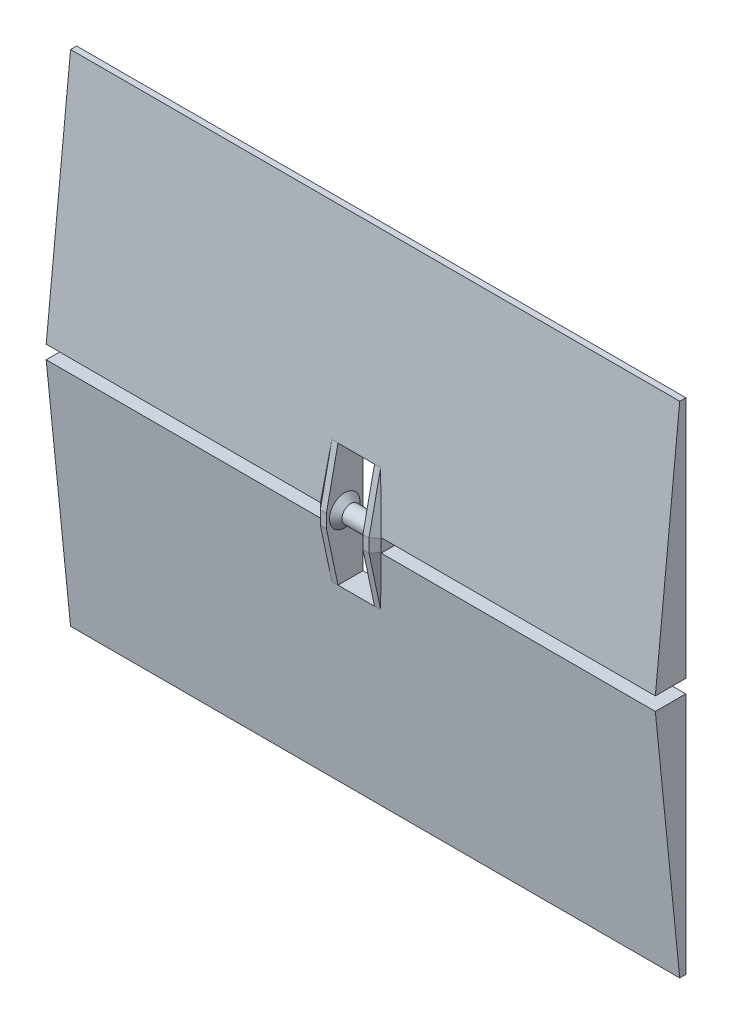
SolidWorks part; units mm, degrees
ref_plane "Płaszczyzna przednia" through (0, 0, 0) normal (0, 0, 1) x (1, 0, 0)
ref_plane "Płaszczyzna górna" through (0, 0, 0) normal (0, 1, 0) x (1, 0, 0)
ref_plane "Płaszczyzna prawa" through (0, 0, 0) normal (1, 0, 0) x (0, 0, -1)
sketch "Szkic1" plane through (0, 0, 0) normal (0, 0, 1) x (1, 0, 0)
  line L2 (-29.6834, 11.2149) -> (-29.6834, -28.6851)
  line L3 (-29.6834, -28.6851) -> (70.3166, -28.6851)
  line L4 (70.3166, 11.2149) -> (70.3166, -28.6851)
  line L11 (15.3166, 11.2149) -> (25.3166, 11.2149)
  line L12 (-29.6834, 11.2149) -> (15.3166, 11.2149)
  line L13 (25.3166, 11.2149) -> (70.3166, 11.2149)
  line L15 (15.3166, 11.2149) -> (25.3166, 11.2149)
  dimension "D1" = 10
extrude "Dodanie-wyciągnięcie1" add sketch "Szkic1" along normal blind 1
sketch "Szkic2" plane through (-29.6834, 0, 0) normal (-1, 0, 0) x (0, 0, 1)
  line L0 (1, 11.2149) -> (5, 11.2149)
  line L1 (5, 11.2149) -> (1, -28.6851)
  line L2 (1, -28.6851) -> (1, 11.2149)
extrude "Dodanie-wyciągnięcie2" add sketch "Szkic2" against normal blind 100
sketch "Szkic3" plane through (0, 0, 0) normal (0, 0, -1) x (-1, 0, 0)
  line L0 (-70.3166, 11.2149) -> (-23.3166, 11.2149) construction
  line L1 (29.6834, 11.2149) -> (-70.3166, 11.2149) construction
  line L2 (-23.3166, 11.2149) -> (-17.3166, 11.2149)
  line L3 (-17.3166, 11.2149) -> (29.6834, 11.2149) construction
  line L6 (-23.3166, 11.2149) -> (-23.3166, 2.2149)
  line L7 (-23.3166, 2.2149) -> (-17.3166, 2.2149)
  line L8 (-17.3166, 11.2149) -> (-17.3166, 2.2149)
  dimension "D1" = 6
extrude "Wytnij-wyciągnięcie1" cut sketch "Szkic3" against normal blind 10
sketch "Szkic4" plane through (0, 11.2149, 0) normal (0, 1, 0) x (1, 0, 0)
  line L0 (70.3166, -5) -> (23.3166, -5) construction
  line L1 (23.3166, 0) -> (25.3166, 0)
  line L2 (23.3166, 0) -> (23.3166, -5)
  line L3 (23.3166, -5) -> (25.3166, -5)
  line L4 (25.3166, 0) -> (25.3166, -5)
  line L5 (17.3166, -5) -> (-29.6834, -5) construction
  line L6 (17.3166, 0) -> (15.3166, 0)
  line L7 (17.3166, 0) -> (17.3166, -5)
  line L8 (17.3166, -5) -> (15.3166, -5)
  line L9 (15.3166, 0) -> (15.3166, -5)
extrude "Dodanie-wyciągnięcie3" add sketch "Szkic4" along normal blind 1.1
mirror "Lustro2" about plane through (0, 12.3149, 0) normal (0, 1, 0) of bodies 107
sketch "Szkic7" plane through (23.3166, 0, 0) normal (-1, 0, 0) x (0, 0, 1)
  line L0 (4.0977, 22.4149) -> (5, 13.4149)
  line L1 (5, 13.4149) -> (5, 11.2149)
  line L2 (5, 11.2149) -> (4.0977, 2.2149)
  line L3 (4.0977, 2.2149) -> (6, 11.2149)
  line L4 (6, 11.2149) -> (6, 13.4149)
  line L5 (6, 13.4149) -> (4.0977, 22.4149)
  line L6 (5, 13.4149) -> (6, 13.4149) construction
  line L7 (5, 11.2149) -> (6, 11.2149) construction
extrude "Dodanie-wyciągnięcie5" add sketch "Szkic7" against normal blind 2
sketch "Szkic8" plane through (23.3166, 0, 0) normal (-1, 0, 0) x (0, 0, 1)
  line L0 (0, 12.3149) -> (6, 12.3149) construction
  line L1 (0, 22.4149) -> (0, 2.2149) construction
  line L2 (6, 11.2149) -> (6, 13.4149) construction
  line L3 (3, 22.4149) -> (3, 2.2149) construction
  line L4 (4.0977, 22.4149) -> (0, 22.4149) construction
  line L5 (4.0977, 2.2149) -> (0, 2.2149) construction
  circle A1 centre (3, 12.3149) radius 2.5
  dimension "D1" = 3
ref_plane "Płaszczyzna2" through (22.3166, 0, 0) normal (-1, 0, 0) x (0, 0, 1)
sketch "Szkic9" plane through (22.3166, 0, 0) normal (-1, 0, 0) x (0, 0, 1)
  circle A0 centre (3, 12.3149) radius 1.45
loft "Wyciągnięcie po profilach1" add profiles "Szkic8", "Szkic9"
sketch "Szkic10" plane through (22.3166, 0, 0) normal (-1, 0, 0) x (0, 0, 1)
  circle A0 centre (3, 12.3149) radius 1.45
extrude "Dodanie-wyciągnięcie6" add sketch "Szkic10" along normal blind 2
mirror "Lustro3" about plane through (20.3166, 12.3149, 3) normal (-1, 0, 0) of "Dodanie-wyciągnięcie5", "Wyciągnięcie po profilach1", "Dodanie-wyciągnięcie6"
chamfer "Sfazowanie1" distance 1 angle 45 6 edges at (15.3166, 6.7149, 5.0489) (15.3166, 12.3149, 6) (15.3166, 17.9149, 5.0489) (25.3166, 17.9149, 5.0489) (25.3166, 12.3149, 6) (25.3166, 6.7149, 5.0489)
